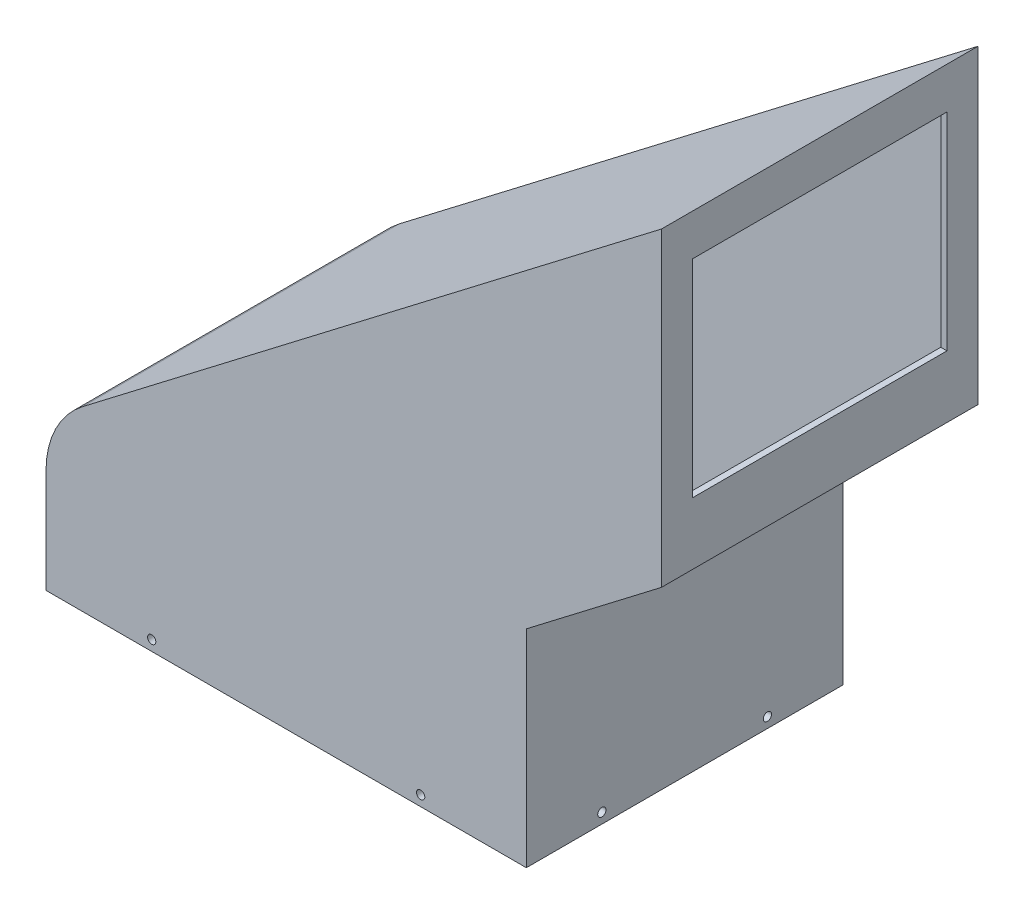
SolidWorks part; units mm, degrees
ref_plane "Plano frontal" through (0, 0, 0) normal (0, 0, 1) x (1, 0, 0)
ref_plane "Plano superior" through (0, 0, 0) normal (0, 1, 0) x (1, 0, 0)
ref_plane "Plano direito" through (0, 0, 0) normal (1, 0, 0) x (0, 0, -1)
sketch "Esboço1" plane through (0, 0, 0) normal (0, 0, 1) x (1, 0, 0)
  line L0 (0, 0) -> (0, 50)
  line L1 (17.6408, 85.7278) -> (297.4538, 300)
  line L2 (297.4538, 300) -> (297.4538, 150)
  line L3 (297.4538, 150) -> (232.16, 100)
  line L5 (232.16, 0) -> (0, 0)
  line L6 (232.16, 100) -> (232.16, 0)
  arc A0 (0, 50) -> (17.6408, 85.7278) centre (45, 50) cw
  dimension "D5" = 45
  dimension "D1" = 100
  dimension "D2" = 50
  dimension "D3" = 150
  dimension "D4" = 300
  dimension "D6" = 232.16
extrude "Ressalto-extrusão1" add sketch "Esboço1" along normal blind 153
shell "Casca1" thickness 3
sketch "Esboço4" plane through (297.4538, 0, 0) normal (1, 0, 0) x (0, 0, -1)
  line L0 (0, 150) -> (0, 300) construction
  line L1 (-138, 280) -> (-15, 280)
  line L2 (-138, 280) -> (-138, 180)
  line L3 (-138, 180) -> (-15, 180)
  line L4 (-15, 280) -> (-15, 180)
  line L5 (-153, 150) -> (-153, 300) construction
  line L6 (-153, 300) -> (0, 300) construction
  dimension "D1" = 15
  dimension "D2" = 15
  dimension "D3" = 20
  dimension "D4" = 100
extrude "Corte-extrusão1" cut sketch "Esboço4" against normal up to next
sketch "Esboço5" plane through (0, 0, 153) normal (0, 0, 1) x (1, 0, 0)
  circle A0 centre (181.08, 5) radius 2
  circle A1 centre (51.08, 5) radius 2
extrude "Corte-extrusão2" cut sketch "Esboço5" against normal through all
sketch "Esboço6" plane through (232.16, 0, 0) normal (1, 0, 0) x (0, 0, -1)
  circle A0 centre (-36.5, 5) radius 2
  circle A1 centre (-116.5, 5) radius 2
  dimension "D1" = 4
  dimension "D2" = 4
extrude "Corte-extrusão3" cut sketch "Esboço6" against normal through all
